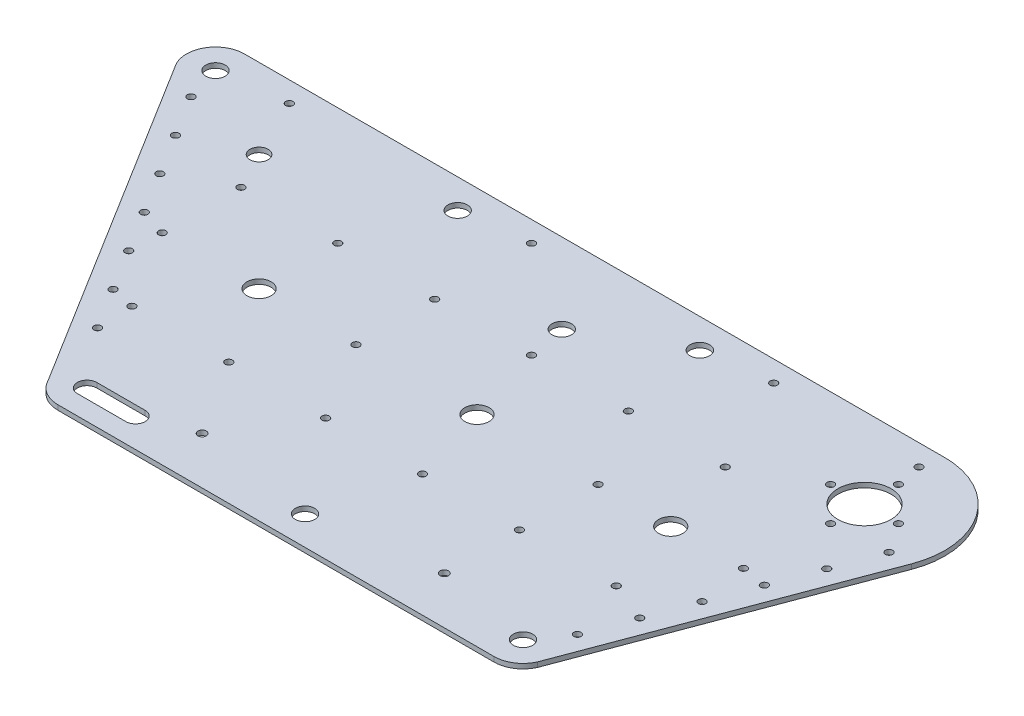
SolidWorks part; units mm, degrees
ref_plane "Front Plane" through (0, 0, 0) normal (0, 0, 1) x (1, 0, 0)
ref_plane "Top Plane" through (0, 0, 0) normal (0, 1, 0) x (1, 0, 0)
ref_plane "Right Plane" through (0, 0, 0) normal (1, 0, 0) x (0, 0, -1)
sketch "Sketch2" plane through (0, 0, 0) normal (0, 1, 0) x (1, 0, 0)
  line L0 (-106.005, 144.9436) -> (182.9628, 145.1972)
  line L1 (160.9924, -19) -> (-18.9986, -19)
  line L2 (171.9007, -12) -> (214.0696, 100.3323)
  line L3 (-18.9986, -3) -> (1.0004, -3)
  line L4 (1.0003, -11) -> (-18.9986, -11)
  line L5 (-29.6999, -12.4286) -> (-116.0853, 126.6112)
  circle A0 centre (182.992, 112) radius 11
  circle A1 centre (-18.9988, 64) radius 5
  circle A2 centre (70.9964, 64) radius 5
  circle A3 centre (150.9927, 64) radius 5
  circle A4 centre (-78.996, 136.5) radius 1.5
  circle A5 centre (20.9989, 136.5) radius 1.5
  circle A6 centre (120.9939, 136.5) radius 1.5
  circle A7 centre (180.9909, 136.5) radius 1.5
  circle A8 centre (170.3325, 6.1186) radius 1.5
  circle A9 centre (177.3307, 24.8545) radius 1.5
  circle A10 centre (184.3286, 43.5896) radius 1.5
  circle A11 centre (191.3265, 62.3248) radius 1.5
  circle A12 centre (198.3244, 81.0602) radius 1.5
  circle A13 centre (-38.3619, 16.6713) radius 1.5
  circle A14 centre (-48.9163, 33.6588) radius 1.5
  circle A15 centre (-59.4708, 50.6466) radius 1.5
  circle A16 centre (-70.0255, 67.6347) radius 1.5
  circle A17 centre (-80.5803, 84.623) radius 1.5
  circle A18 centre (70.9966, -7) radius 4
  circle A19 centre (120.9939, 0.5) radius 1.75
  circle A20 centre (20.9989, 0.5) radius 1.75
  ellipse E0 centre (-105.9945, 133) end of major axis (-105.9945, 137) minor radius 4
  ellipse E1 centre (160.9926, -7) end of major axis (160.9926, -3) minor radius 4
  ellipse E2 centre (-18.9986, -7) end of major axis (-18.9986, -11) minor radius 4 (-18.9986, -3) -> (-18.9986, -11) ccw
  ellipse E3 centre (182.992, 112) end of major axis (182.992, 123) minor radius 11
  ellipse E4 centre (-105.9945, 133) end of major axis (-105.9945, 144.9436) minor radius 11.943 (-106.005, 144.9436) -> (-116.0853, 126.6112) ccw
  ellipse E5 centre (182.992, 112) end of major axis (182.992, 145.1972) minor radius 33.1955 (214.0696, 100.3323) -> (182.9628, 145.1972) ccw
  ellipse E6 centre (1.0003, -7) end of major axis (1.0004, -3) minor radius 4 (1.0003, -11) -> (1.0004, -3) ccw
  ellipse E7 centre (182.9908, 126) end of major axis (182.9908, 127.5) minor radius 1.4999
  ellipse E8 centre (196.9901, 112) end of major axis (196.9901, 113.5) minor radius 1.4999
  ellipse E9 centre (168.9915, 112) end of major axis (168.9915, 113.5) minor radius 1.4999
  ellipse E10 centre (182.9908, 98) end of major axis (182.9908, 99.5) minor radius 1.4999
  ellipse E11 centre (-18.9986, -7) end of major axis (-18.9986, -19) minor radius 11.9993 (-29.6999, -12.4286) -> (-18.9986, -19) ccw
  ellipse E12 centre (160.9926, -7) end of major axis (160.9926, 5) minor radius 11.9994 (160.9924, -19) -> (171.9007, -12) ccw
  ellipse E15 centre (120.9939, 64) end of major axis (120.994, 65.5) minor radius 1.4999
  ellipse E16 centre (20.9989, 64) end of major axis (20.9989, 65.5) minor radius 1.4999
  ellipse E17 centre (-58.997, 64) end of major axis (-58.997, 65.5) minor radius 1.4999
  ellipse E18 centre (180.9909, 64) end of major axis (180.9909, 65.5) minor radius 1.4999
  ellipse E22 centre (60.9969, 96.5) end of major axis (60.9969, 98) minor radius 1.4999
  ellipse E23 centre (140.9929, 96.5) end of major axis (140.9929, 98) minor radius 1.4999
  ellipse E24 centre (160.992, 31.5) end of major axis (160.992, 33) minor radius 1.4999
  ellipse E25 centre (80.996, 31.5) end of major axis (80.996, 33) minor radius 1.4999
  ellipse E26 centre (-18.9991, 96.5) end of major axis (-18.9991, 98) minor radius 1.4999
  ellipse E27 centre (-38.998, 31.5) end of major axis (-38.998, 33) minor radius 1.4999
  ellipse E31 centre (-101.6892, 118.5984) end of major axis (-101.6892, 120.0984) minor radius 1.4999
  ellipse E32 centre (-91.1347, 101.6106) end of major axis (-91.1347, 103.1106) minor radius 1.4999
  ellipse E38 centre (205.3225, 99.7958) end of major axis (205.3225, 101.2958) minor radius 1.4999
  ellipse E45 centre (20.9989, 96.5) end of major axis (20.9989, 98) minor radius 1.4999
  ellipse E46 centre (100.995, 96.5) end of major axis (100.995, 98) minor radius 1.4999
  ellipse E47 centre (-58.9971, 96.5) end of major axis (-58.997, 98) minor radius 1.4999
  ellipse E48 centre (0.9999, 31.5) end of major axis (1, 33) minor radius 1.4999
  ellipse E49 centre (40.9979, 31.5) end of major axis (40.9979, 33) minor radius 1.4999
  ellipse E50 centre (120.9939, 31.5) end of major axis (120.994, 33) minor radius 1.4999
  ellipse E51 centre (-66.9967, 112) end of major axis (-66.9966, 115.75) minor radius 3.7498
  ellipse E52 centre (57.9973, 112) end of major axis (53.9973, 112) minor radius 4
  ellipse E53 centre (-5.9995, 133) end of major axis (-5.9995, 137) minor radius 4
  ellipse E54 centre (93.9954, 133) end of major axis (93.9954, 137) minor radius 4
  dimension "D1" = 22
  dimension "D2" = 10
  dimension "D3" = 10
  dimension "D4" = 10
  dimension "D5" = 3
  dimension "D6" = 3
  dimension "D7" = 3
  dimension "D8" = 3
  dimension "D9" = 3
  dimension "D10" = 3
  dimension "D11" = 3
  dimension "D12" = 3
  dimension "D13" = 3
  dimension "D14" = 3
  dimension "D15" = 3
  dimension "D16" = 3
  dimension "D17" = 3
  dimension "D18" = 3
  dimension "D19" = 8
  dimension "D20" = 3.5
extrude "Boss-Extrude1" add sketch "Sketch2" along normal blind 2
